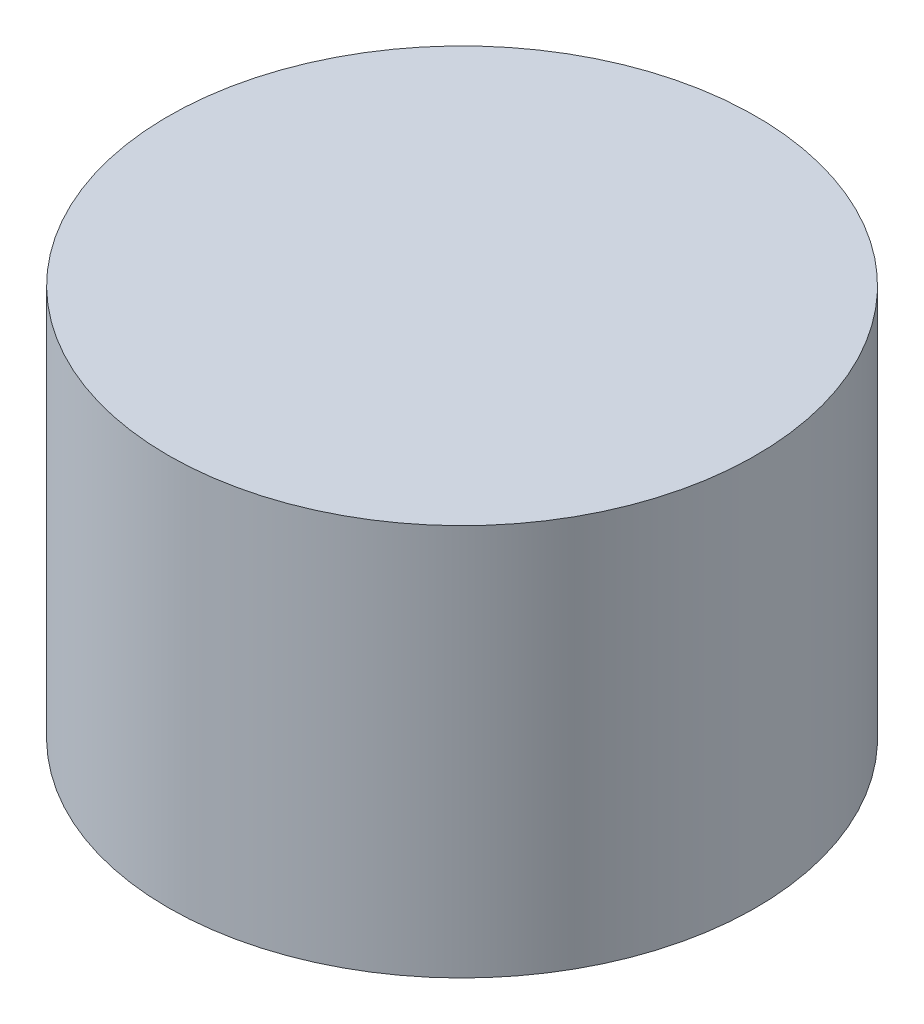
SolidWorks part; units mm, degrees
ref_plane "Front Plane" through (0, 0, 0) normal (0, 0, 1) x (1, 0, 0)
ref_plane "Top Plane" through (0, 0, 0) normal (0, 1, 0) x (1, 0, 0)
ref_plane "Right Plane" through (0, 0, 0) normal (1, 0, 0) x (0, 0, -1)
sketch "Sketch1" plane through (0, 0, 0) normal (0, 1, 0) x (1, 0, 0)
  circle A0 centre (0, 0) radius 7.5
  point P2 (0, 0)
  dimension "D1" = 15
extrude "Boss-Extrude1" add sketch "Sketch1" along normal blind 10
